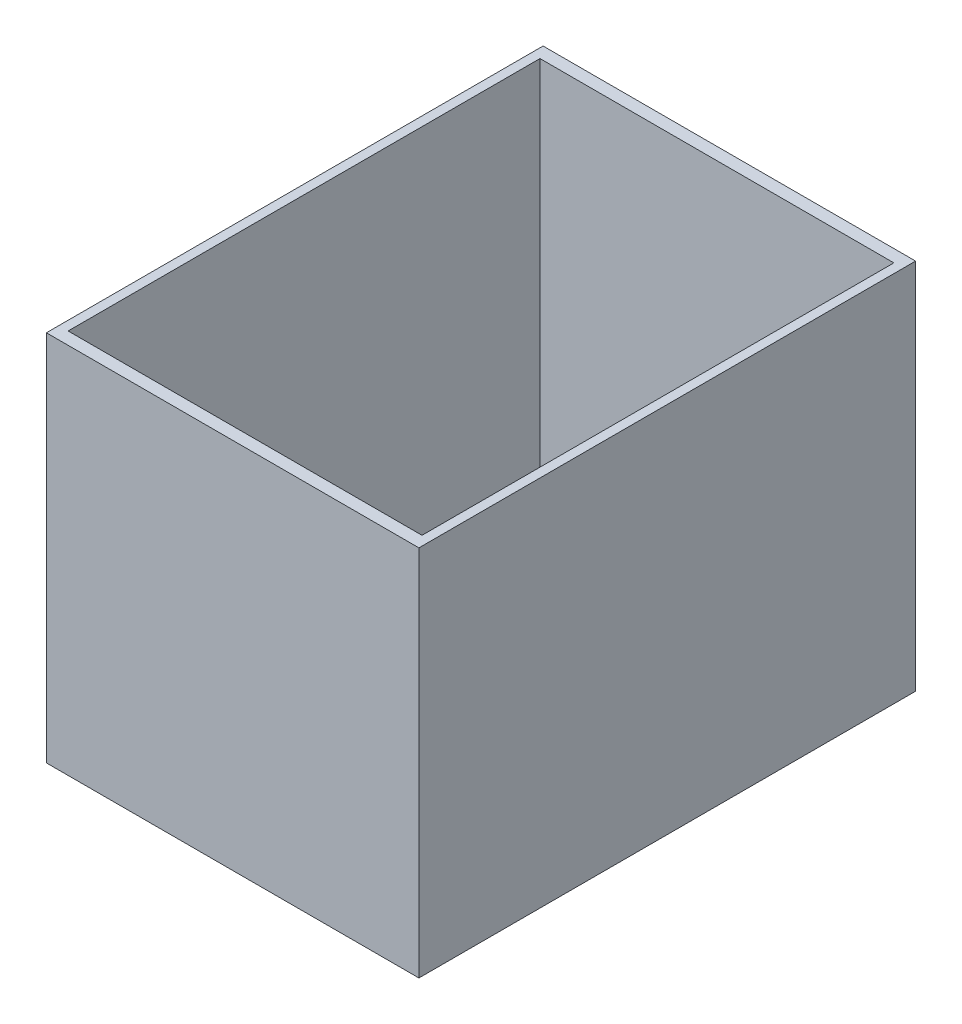
SolidWorks part; units mm, degrees
ref_plane "Front Plane" through (0, 0, 0) normal (0, 0, 1) x (1, 0, 0)
ref_plane "Top Plane" through (0, 0, 0) normal (0, 1, 0) x (1, 0, 0)
ref_plane "Right Plane" through (0, 0, 0) normal (1, 0, 0) x (0, 0, -1)
sketch "Sketch1" plane through (0, 0, 0) normal (0, 1, 0) x (1, 0, 0)
  line L1 (15, -20) -> (-15, -20)
  line L2 (15, -20) -> (15, 20)
  line L3 (15, 20) -> (-15, 20)
  line L4 (-15, -20) -> (-15, 20)
  line L5 (15, -20) -> (-15, 20) construction
  line L6 (15, 20) -> (-15, -20) construction
  line L7 (14.25, -19) -> (-14.25, -19)
  line L8 (14.25, -19) -> (14.25, 19)
  line L9 (14.25, 19) -> (-14.25, 19)
  line L10 (-14.25, -19) -> (-14.25, 19)
  line L11 (14.25, -19) -> (-14.25, 19) construction
  line L12 (14.25, 19) -> (-14.25, -19) construction
  point P0 (0, 0)
  point P5 (0, 0)
  dimension "D1" = 30
  dimension "D2" = 40
  dimension "D3" = 38
extrude "Boss-Extrude1" add sketch "Sketch1" along normal blind 30
equation "\"D3@Sketch1\"=\"D2@Sketch1\"-2"
